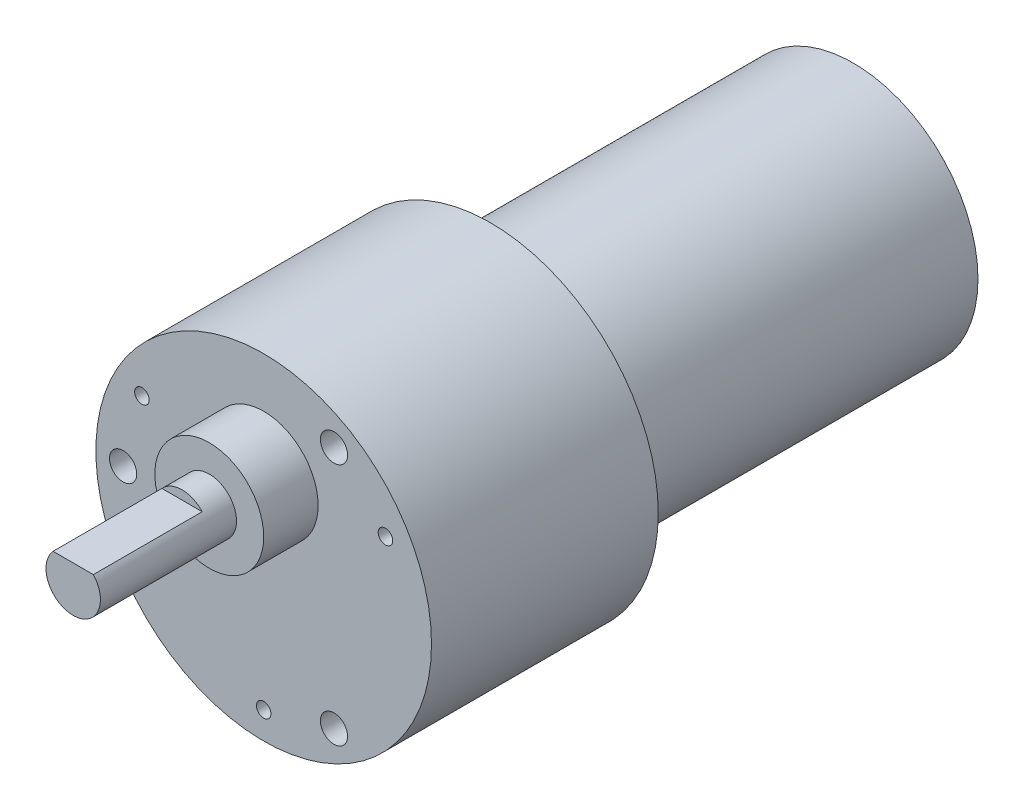
SolidWorks part; units mm, degrees
ref_plane "正面" through (0, 0, 0) normal (0, 0, 1) x (1, 0, 0)
ref_plane "平面" through (0, 0, 0) normal (0, 1, 0) x (1, 0, 0)
ref_plane "右側面" through (0, 0, 0) normal (1, 0, 0) x (0, 0, -1)
sketch "ｽｹｯﾁ2" plane through (0, 0, 0) normal (0, 0, 1) x (1, 0, 0)
  circle A0 centre (0, 0) radius 13.75
extrude "ﾎﾞｽ - 押し出し1" add sketch "ｽｹｯﾁ2" along normal blind 40
sketch "ｽｹｯﾁ3" plane through (0, 0, 40) normal (0, 0, 1) x (1, 0, 0)
  circle A0 centre (0, 0) radius 18.5
extrude "ﾎﾞｽ - 押し出し2" add sketch "ｽｹｯﾁ3" along normal blind 25
chamfer "面取り1" distance 2 angle 45 1 edges at (13.75, 0, 40)
sketch "ｽｹｯﾁ4" plane through (0, 0, 65) normal (0, 0, 1) x (1, 0, 0)
  line L0 (0, -15.125) -> (0, 15.125) construction
  circle A0 centre (0, 7) radius 6
extrude "ﾎﾞｽ - 押し出し3" add sketch "ｽｹｯﾁ4" along normal blind 6
sketch "ｽｹｯﾁ5" plane through (0, 0, 71) normal (0, 0, 1) x (1, 0, 0)
  circle A0 centre (0, 7) radius 3
extrude "ﾎﾞｽ - 押し出し4" add sketch "ｽｹｯﾁ5" along normal blind 15
sketch "ｽｹｯﾁ6" plane through (0, 0, 86) normal (0, 0, 1) x (1, 0, 0)
  line L0 (-2.2225, 9.0151) -> (2.2225, 9.0151)
  circle A0 centre (0, 7) radius 3 construction
  arc A1 (2.2225, 9.0151) -> (-2.2225, 9.0151) centre (0, 7) ccw
extrude "ｶｯﾄ - 押し出し1" cut sketch "ｽｹｯﾁ6" against normal blind 12
sketch "ｽｹｯﾁ7" plane through (0, 0, 65) normal (0, 0, 1) x (1, 0, 0)
  circle A0 centre (-15.5, 0) radius 1.5
extrude "ｶｯﾄ - 押し出し2" cut sketch "ｽｹｯﾁ7" against normal blind 6
sketch "ｽｹｯﾁ8" plane through (0, 0, 65) normal (0, 0, 1) x (1, 0, 0)
  arc A0 (-15.5, 0) -> (7.75, -13.4234) centre (0, 0) ccw
  circle A1 centre (7.75, -13.4234) radius 1.5
extrude "ｶｯﾄ - 押し出し3" cut sketch "ｽｹｯﾁ8" against normal blind 6 contours A1
sketch "ｽｹｯﾁ10" plane through (0, 0, 65) normal (0, 0, 1) x (1, 0, 0)
  arc A0 (7.75, -13.4234) -> (7.75, 13.4234) centre (0, 0) ccw
  circle A1 centre (7.75, 13.4234) radius 1.5
extrude "ｶｯﾄ - 押し出し4" cut sketch "ｽｹｯﾁ10" against normal blind 6 contours A1
sketch "ｽｹｯﾁ11" plane through (0, 0, 0) normal (0, 0, -1) x (-1, 0, 0)
  circle A0 centre (0, 0) radius 5.1
extrude "ﾎﾞｽ - 押し出し5" add sketch "ｽｹｯﾁ11" along normal blind 3
sketch "ｽｹｯﾁ12" plane through (0, 0, 65) normal (0, 0, 1) x (1, 0, 0)
  line L0 (0, -15.5) -> (-13.4234, 7.75) construction
  line L1 (-13.4234, 7.75) -> (13.4234, 7.75) construction
  line L2 (13.4234, 7.75) -> (0, -15.5) construction
  circle A0 centre (0, 0) radius 15.5 construction
  dimension "D1" = 31
hole_wizard "M2x0.4 ねじ穴1" positions "ｽｹｯﾁ13" profile "ｽｹｯﾁ14" tap size "M2x0.4" standard "JIS"
sketch "ｽｹｯﾁ13" plane through (0, 0, 65) normal (0, 0, 1) x (1, 0, 0)
  point P0 (-13.4234, 7.75)
  point P3 (0, -15.5)
  point P6 (13.4234, 7.75)
sketch "ｽｹｯﾁ14" plane through (-13.4234, 7.75, 65) normal (1, 0, 0) x (0, -1, 0)
  line L0 (0, 0) -> (0, 6.4807)
  line L1 (0, 6.4807) -> (0.8, 6)
  line L2 (0.8, 6) -> (0.8, 0)
  line L5 (0.8, 0) -> (0, 0)
  line L10 (0, 6.4807) -> (-0.8, 6) construction
  line L11 (0, -6.35) -> (0, 107.95) construction
  dimension "ねじ下穴ﾄﾞﾘﾙ直径" = 1.6
  dimension "ねじ下穴ﾄﾞﾘﾙの深さ" = 6
  dimension "ﾄﾞﾘﾙ角度" = 118
cosmetic thread "穴のねじ山1"
cosmetic thread "穴のねじ山2"
cosmetic thread "穴のねじ山3"
